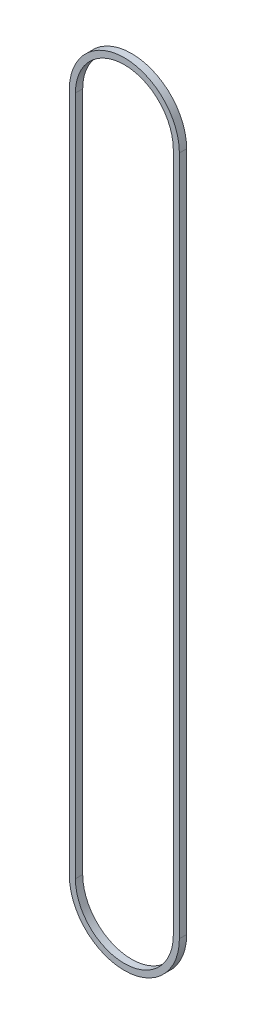
SolidWorks part; units mm, degrees
ref_plane "Front Plane" through (0, 0, 0) normal (0, 0, 1) x (1, 0, 0)
ref_plane "Top Plane" through (0, 0, 0) normal (0, 1, 0) x (1, 0, 0)
ref_plane "Right Plane" through (0, 0, 0) normal (1, 0, 0) x (0, 0, -1)
sketch "Sketch1" plane through (0, 0, 0) normal (0, 0, 1) x (1, 0, 0)
  line L0 (0, 0) -> (0, 711.2) construction
  line L1 (-57.4929, 0) -> (-57.4929, 711.2)
  line L2 (57.4929, 0) -> (57.4929, 711.2)
  line L3 (-51.1429, 0) -> (-51.1429, 711.2)
  line L4 (51.1429, 0) -> (51.1429, 711.2)
  arc A0 (-57.4929, 0) -> (57.4929, 0) centre (0, 0) ccw
  arc A1 (57.4929, 711.2) -> (-57.4929, 711.2) centre (0, 711.2) ccw
  arc A2 (51.1429, 711.2) -> (-51.1429, 711.2) centre (0, 711.2) ccw
  arc A3 (-51.1429, 0) -> (51.1429, 0) centre (0, 0) ccw
  point P3 (0, 355.6)
  dimension "D1" = 57.4929
  dimension "D2" = 711.2
  dimension "D3" = 6.35
extrude "Boss-Extrude1" add sketch "Sketch1" along normal blind 7.62
